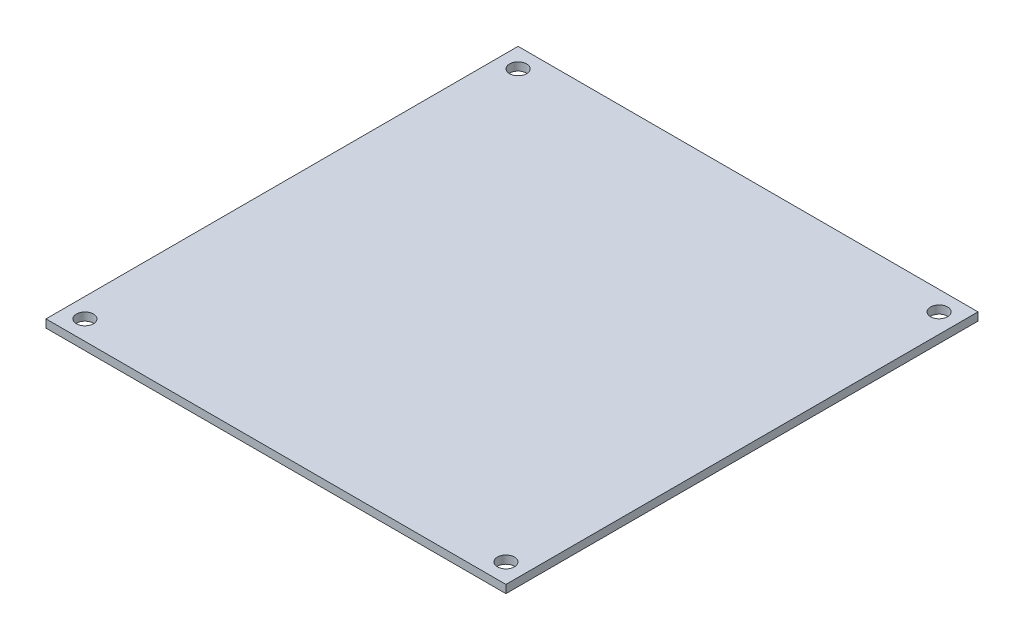
SolidWorks part; units mm, degrees
ref_plane "Front Plane" through (0, 0, 0) normal (0, 0, 1) x (1, 0, 0)
ref_plane "Top Plane" through (0, 0, 0) normal (0, 1, 0) x (1, 0, 0)
ref_plane "Right Plane" through (0, 0, 0) normal (1, 0, 0) x (0, 0, -1)
sketch "Sketch1" plane through (0, 0, 0) normal (0, 1, 0) x (1, 0, 0)
  line L1 (0, 0) -> (94.5, 0)
  line L2 (0, 0) -> (0, 97)
  line L3 (0, 97) -> (94.5, 97)
  line L4 (94.5, 0) -> (94.5, 97)
  dimension "D1" = 94.5
  dimension "D2" = 97
extrude "Boss-Extrude1" add sketch "Sketch1" along normal blind 1.65
sketch "Sketch2" plane through (0, 1.65, 0) normal (0, 1, 0) x (1, 0, 0)
  line L0 (94.5, 0) -> (94.5, 97) construction
  line L1 (4, 93) -> (90.5, 93) construction
  line L2 (4, 93) -> (4, 4) construction
  line L3 (4, 4) -> (90.5, 4) construction
  line L4 (90.5, 93) -> (90.5, 4) construction
  line L5 (0, 0) -> (94.5, 0) construction
  line L6 (0, 97) -> (0, 0) construction
  line L7 (94.5, 97) -> (0, 97) construction
  circle A0 centre (4, 93) radius 1.75
  circle A1 centre (90.5, 93) radius 1.75
  circle A2 centre (90.5, 4) radius 1.75
  circle A3 centre (4, 4) radius 1.75
  dimension "D5" = 3.5
  dimension "D6" = 3.5
  dimension "D7" = 3.5
  dimension "D8" = 3.5
  dimension "D1" = 4
  dimension "D2" = 4
  dimension "D3" = 4
  dimension "D4" = 4
extrude "Cut-Extrude1" cut sketch "Sketch2" against normal through all
sketch "Sketch3" plane through (0, 1.65, 0) normal (0, 1, 0) x (1, 0, 0)
  line L0 (6.9372, 67.7827) -> (85.9961, 67.7827)
  line L1 (26.5211, 59.2862) -> (74.306, 59.2862)
  line L2 (26.5211, 59.2862) -> (26.5211, 41.51)
  line L3 (26.5211, 41.51) -> (74.306, 41.51)
  line L4 (74.306, 59.2862) -> (74.306, 41.51)
  line L5 (6.9372, 34.279) -> (85.9961, 34.279)
